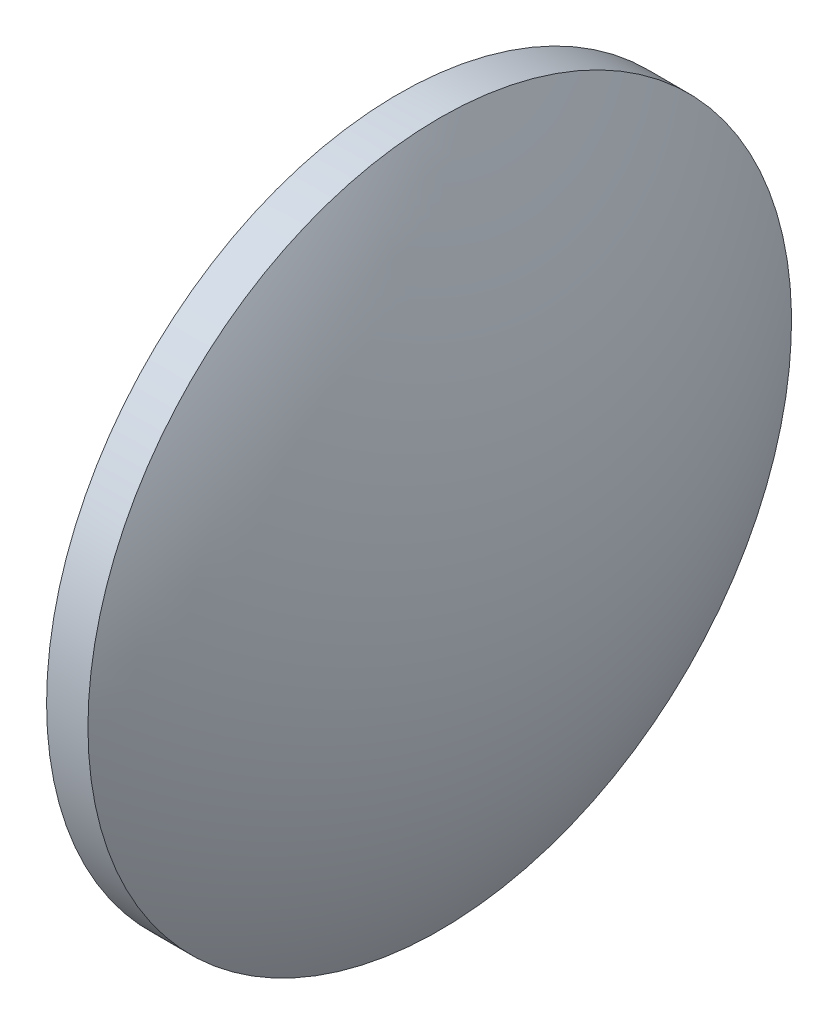
SolidWorks part; units mm, degrees
ref_plane "前视基准面" through (0, 0, 0) normal (0, 0, 1) x (1, 0, 0)
ref_plane "上视基准面" through (0, 0, 0) normal (0, 1, 0) x (1, 0, 0)
ref_plane "右视基准面" through (0, 0, 0) normal (1, 0, 0) x (0, 0, -1)
sketch "草图1" plane through (0, 0, 0) normal (0, 0, 1) x (1, 0, 0)
  line L0 (529.2401, 140.6811) -> (542.6859, 140.6811) construction
  line L1 (533.9822, 140.6811) -> (533.9822, 153.1811)
  line L2 (538.6822, 140.6811) -> (533.9822, 140.6811)
  line L5 (533.9822, 153.1811) -> (535.4522, 153.1811)
  arc A0 (538.6822, 140.6811) -> (535.4522, 153.1811) centre (512.8798, 140.6811) ccw
revolve "旋转1" add sketch "草图1" angle 360 about L0
